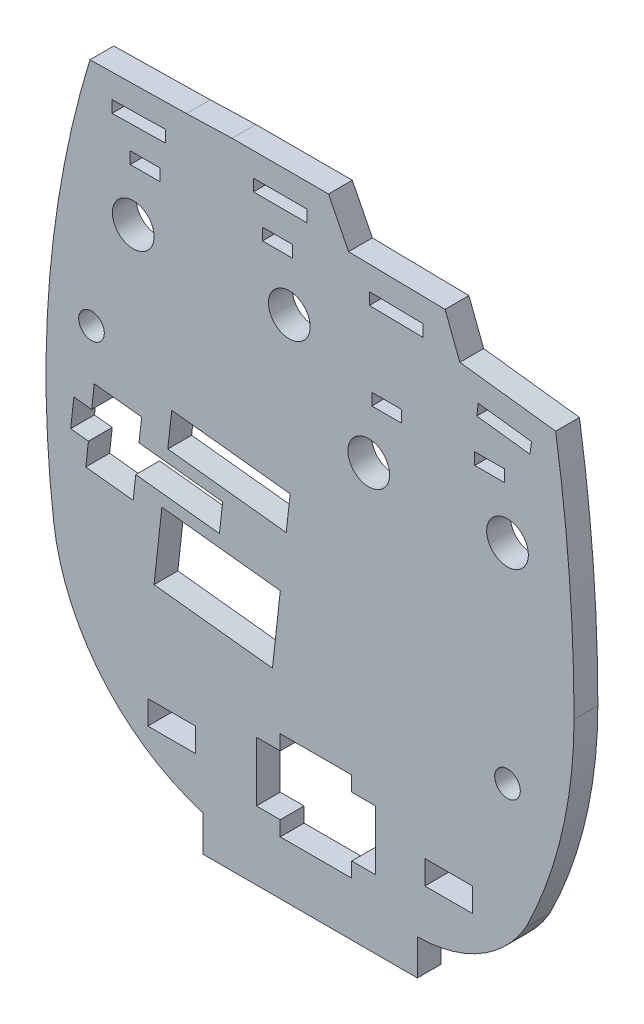
SolidWorks part; units mm, degrees
ref_plane "Front Plane" through (0, 0, 0) normal (0, 0, 1) x (1, 0, 0)
ref_plane "Top Plane" through (0, 0, 0) normal (0, 1, 0) x (1, 0, 0)
ref_plane "Right Plane" through (0, 0, 0) normal (1, 0, 0) x (0, 0, -1)
sketch "Sketch1" plane through (0, 0, 0) normal (0, 0, 1) x (1, 0, 0)
  line L0 (-4.5, 78.51) -> (-4.5, 76.51)
  line L1 (4.5, 78.51) -> (-4.5, 78.51)
  line L2 (-4.5, 76.51) -> (4.5, 76.51)
  line L3 (4.5, 76.51) -> (4.5, 78.51)
  line L4 (-4, -2.5) -> (0, -2.5)
  line L5 (0, 0) -> (19.57, 0) construction
  line L6 (0, 0) -> (0, 82.51) construction
  line L7 (12, 0) -> (0, 0)
  line L8 (0, 0) -> (-23.845, 0) construction
  line L9 (32.6473, 57.3216) -> (37.6473, 57.3216)
  line L10 (-12.9786, -18) -> (-12.9786, -24)
  line L11 (32.6473, 55.3216) -> (37.6473, 55.3216)
  line L12 (37.6473, 55.3216) -> (37.6473, 57.3216)
  line L13 (32.6473, 57.3216) -> (32.6473, 55.3216)
  line L14 (-28.275, 78.0626) -> (-19.2763, 78.2186)
  line L15 (-28.275, 78.0626) -> (-28.2403, 76.0629)
  line L16 (-28.2403, 76.0629) -> (-19.2416, 76.2189)
  line L17 (-19.2416, 76.2189) -> (-19.2763, 78.2186)
  line L18 (15.3631, 57.3216) -> (20.3631, 57.3216)
  line L19 (15.3631, 55.3216) -> (20.3631, 55.3216)
  line L20 (20.3631, 55.3216) -> (20.3631, 57.3216)
  line L21 (15.3631, 57.3216) -> (15.3631, 55.3216)
  line L22 (-2.9786, 72.1512) -> (2.0214, 72.1512)
  line L23 (15.0008, 71.7441) -> (14.9659, 69.7445)
  line L24 (14.9659, 69.7445) -> (23.9646, 69.5874)
  line L25 (-2.9786, 70.1512) -> (2.0214, 70.1512)
  line L26 (23.9995, 71.5871) -> (15.0008, 71.7441)
  line L27 (23.9646, 69.5874) -> (23.9995, 71.5871)
  line L28 (-23.845, 0) -> (-23.845, 82.14) construction
  line L29 (2.0214, 70.1512) -> (2.0214, 72.1512)
  line L30 (30.1504, 69.0671) -> (46.2296, 67.0929)
  line L31 (-2.9786, 72.1512) -> (-2.9786, 70.1512)
  line L32 (42.169, 63.5614) -> (33.236, 64.6582)
  line L33 (1.6675, 35.7056) -> (1.0057, 29.7422)
  line L34 (33.236, 64.6582) -> (32.9923, 62.6731)
  line L35 (-25.179, 72.1512) -> (-20.179, 72.1512)
  line L36 (19.57, 0) -> (19.57, 75.665) construction
  line L37 (0, 0) -> (38.19, 0) construction
  line L38 (-25.179, 70.1512) -> (-20.179, 70.1512)
  line L39 (32.9923, 62.6731) -> (41.9253, 61.5763)
  line L40 (-20.179, 70.1512) -> (-20.179, 72.1512)
  line L41 (-25.179, 72.1512) -> (-25.179, 70.1512)
  line L42 (41.9253, 61.5763) -> (42.169, 63.5614)
  line L43 (1.6675, 35.7056) -> (-18.2105, 37.9113)
  line L44 (0.0132, 20.7971) -> (-1.3102, 8.8703)
  line L45 (12, 0) -> (12, -2.5)
  line L46 (-18.8723, 31.9479) -> (1.0057, 29.7422)
  line L47 (12, -15) -> (0, -15)
  line L48 (-10.203, 23.9883) -> (-9.6615, 28.8683)
  line L49 (-35.1782, 26.7596) -> (-34.6367, 31.6396)
  line L50 (-9.6615, 28.8683) -> (-23.7053, 30.4266)
  line L51 (-32.6391, 22.4533) -> (-32.198, 26.4289)
  line L52 (-35.1782, 26.7596) -> (-32.198, 26.4289)
  line L53 (-24.2468, 25.5466) -> (-10.203, 23.9883)
  line L54 (-23.7053, 30.4266) -> (-23.2642, 34.4022)
  line L55 (-24.6879, 21.571) -> (-32.6391, 22.4533)
  line L56 (-18.8723, 31.9479) -> (-18.2105, 37.9113)
  line L57 (-31.2154, 35.2845) -> (-31.6565, 31.3089)
  line L58 (-23.2642, 34.4022) -> (-31.2154, 35.2845)
  line L59 (-31.6565, 31.3089) -> (-34.6367, 31.6396)
  line L60 (-24.6879, 21.571) -> (-24.2468, 25.5466)
  line L61 (-19.8648, 23.0028) -> (0.0132, 20.7971)
  line L62 (-21.1882, 11.076) -> (-1.3102, 8.8703)
  line L63 (0, -15) -> (0, -12.5)
  line L64 (-4, -12.5) -> (-4, -2.5)
  line L65 (-19.8648, 23.0028) -> (-21.1882, 11.076)
  line L66 (-12.9786, -24) -> (23.0214, -24)
  line L67 (-4, -12.5) -> (0, -12.5)
  line L68 (0, -2.5) -> (0, 0)
  line L69 (16, -12.5) -> (12, -12.5)
  line L70 (16, -12.5) -> (16, -2.5)
  line L71 (16, -2.5) -> (12, -2.5)
  line L72 (12, -12.5) -> (12, -15)
  line L73 (23.0214, -24) -> (23.0214, -18)
  line L74 (38.19, 0) -> (38.19, 68.08) construction
  line L75 (11.4712, 75.8064) -> (27.6688, 75.5236)
  line L76 (-8.1, 82.51) -> (8.1, 82.51)
  line L77 (-15.7462, 82.2805) -> (-31.9438, 81.9995)
  line L78 (30.1504, 69.0671) -> (27.6688, 75.5236)
  line L79 (-9.9323, 26.4283) -> (3.8676, 24.897) construction
  line L80 (41.2436, -7.5) -> (16, -7.5) construction
  line L81 (11.4712, 75.8064) -> (8.1, 82.51)
  line L82 (-8.1, 82.51) -> (-15.7462, 82.2805)
  line L83 (-35.1782, 26.7596) -> (49.3139, 26.7596) construction
  line L84 (37.7025, 64.1098) -> (38.19, 68.08) construction
  line L85 (38.1473, 11.8216) -> (-38.0327, 11.8216) construction
  line L86 (-18.8723, 31.9479) -> (-19.8648, 23.0028) construction
  line L87 (-19.3685, 27.4754) -> (-39.2913, 29.686) construction
  line L88 (19.5002, 71.6656) -> (19.57, 75.665) construction
  line L89 (-23.7756, 78.1406) -> (-23.845, 82.14) construction
  line L90 (0, 78.51) -> (0, 82.51) construction
  line L91 (38.1473, 46.8216) -> (38.1473, 11.8216) construction
  arc A0 (23.0214, -18) -> (41.2436, -7.5) centre (23.0214, 3.0618) ccw
  circle A1 centre (38.1473, 11.8216) radius 2.15
  arc A2 (-38.0327, 11.8216) -> (-31.9438, 81.9995) centre (129.7414, 32.618) cw
  circle A3 centre (-24.679, 61.6512) radius 3.5
  circle A4 centre (1.5214, 61.6512) radius 3.5
  circle A5 centre (14.8631, 46.8216) radius 3.5
  circle A6 centre (38.1473, 46.8216) radius 3.5
  arc A7 (-38.0327, 11.8216) -> (-12.9786, -18) centre (-2.5175, 16.2239) ccw
  circle A8 centre (-31.6815, 43.4564) radius 2.15
  circle A9 centre (-14, -9.1244) radius 2.15 construction
  arc A10 (49.3139, 26.7596) -> (41.2436, -7.5) centre (-27.4393, 26.7596) cw
  arc A11 (49.3139, 26.7596) -> (46.2296, 67.0929) centre (-215.9488, 26.7596) ccw
  dimension "D1" = 7
  dimension "D15" = 23.845
  dimension "D16" = 82.14
  dimension "D21" = 18
  dimension "D22" = 14.8631
  dimension "D23" = 68.08
  dimension "D24" = 4
  dimension "D27" = 5
  dimension "D28" = 23.0214
  dimension "D29" = 55.3216
  dimension "D30" = 32.6473
  dimension "D39" = 25.179
  dimension "D40" = 9.6615
  dimension "D41" = 10.203
  dimension "D42" = 12.9786
  dimension "D43" = 14
  dimension "D44" = 35
  dimension "D47" = 57.3216
  dimension "D48" = 4
  dimension "D65" = 61.6512
  dimension "D72" = 9.1244
  dimension "D61" = 46.8216
  dimension "D62" = 2
  dimension "D53" = 9.0001
  dimension "D2" = 4.3
  dimension "D8" = 12
  dimension "D14" = 10
  dimension "D9" = 9
  dimension "D10" = 1.0057
  dimension "D11" = 1.5214
  dimension "D12" = 6
  dimension "D13" = 82.51
  dimension "D17" = 19.57
  dimension "D18" = 2.5
  dimension "D19" = 75.665
  dimension "D20" = 38.19
  dimension "D25" = 4
  dimension "D26" = 16.2
  dimension "D32" = 15.3631
  dimension "D33" = 70.1512
  dimension "D34" = 8.1
  dimension "D35" = 38.1473
  dimension "D36" = 2.9786
  dimension "D37" = 4
  dimension "D38" = 4.91
  dimension "D45" = 20
  dimension "D46" = 4
  dimension "D49" = 4.5
  dimension "D50" = 24.679
  dimension "D51" = 25.1285
  dimension "D52" = 31.6815
  dimension "D54" = 8
  dimension "D56" = 14.13
  dimension "D57" = 72.1512
  dimension "D59" = 21.571
  dimension "D60" = 43.4564
  dimension "ThumbLinkLengthMCP" = 20.045
extrude "Boss-Extrude1" add sketch "Sketch1" along normal blind 4
sketch "Sketch2" plane through (0, 0, 0) normal (0, 0, -1) x (-1, 0, 0)
  line L0 (-5.0214, -24) -> (-5.0214, -5.2587) construction
  line L1 (-24.2714, -10) -> (-32.2714, -10)
  line L2 (-32.2714, -10) -> (-32.2714, -6)
  line L3 (-32.2714, -6) -> (-24.2714, -6)
  line L4 (-24.2714, -6) -> (-24.2714, -10)
  line L5 (12.9786, -24) -> (-23.0214, -24) construction
  line L6 (14.2286, -6) -> (14.2286, -10)
  line L7 (22.2286, -6) -> (14.2286, -6)
  line L8 (22.2286, -10) -> (22.2286, -6)
  line L9 (14.2286, -10) -> (22.2286, -10)
  dimension "D1" = 4
  dimension "D2" = 8
  dimension "D3" = 19.25
  dimension "D4" = 14
extrude "Cut-Extrude1" cut sketch "Sketch2" against normal through all
equation "\"D13@Sketch1\"= \"HL@parametersSketch@prostheticParameters.SLDPRT\" * 0.446'Middle Base Frame"
equation "\"D15@Sketch1\"= \"HB@parametersSketch@prostheticParameters.SLDPRT\" * 0.251'Index Base Frame X"
equation "\"D16@Sketch1\"= \"HL@parametersSketch@prostheticParameters.SLDPRT\" * 0.444'Index Base Frame Y"
equation "\"D17@Sketch1\"= \"HB@parametersSketch@prostheticParameters.SLDPRT\" * 0.206'Ring Base Frame X"
equation "\"D19@Sketch1\"= \"HL@parametersSketch@prostheticParameters.SLDPRT\" * 0.409'Ring base Frame Y"
equation "\"D20@Sketch1\"= \"HB@parametersSketch@prostheticParameters.SLDPRT\" * 0.402'Pinky Base Frame X"
equation "\"D23@Sketch1\"= \"HL@parametersSketch@prostheticParameters.SLDPRT\" * 0.368'Pinky Base Frame Y"
equation "\"D26@Sketch1\"= \"fingerWidth@parametersSketch@prostheticParameters.SLDPRT\"'Fingers Width"
equation "\"D59@Sketch1\"= \"HL@parametersSketch@prostheticParameters.SLDPRT\" * 0.1166'Hole Thumb Y"
equation "\"D40@Sketch1\"= \"HB@parametersSketch@prostheticParameters.SLDPRT\" * 0.1017'Hole Thumb X1"
equation "\"D41@Sketch1\"= \"HB@parametersSketch@prostheticParameters.SLDPRT\" * 0.1074'Hole Thumb X2"
equation "\"ThumbLinkLengthMCP@Sketch1\"= \"HB@parametersSketch@prostheticParameters.SLDPRT\" * 0.211"
equation "\"D53@Sketch1\"= \"fingerWidth@parametersSketch@prostheticParameters.SLDPRT\" * 0.55556"
equation "\"D34@Sketch1\"= \"fingerWidth@parametersSketch@prostheticParameters.SLDPRT\" / 2"
equation "\"D2@Sketch1\"= 4 + \"tol1@parametersSketch@prostheticParameters.SLDPRT\""
